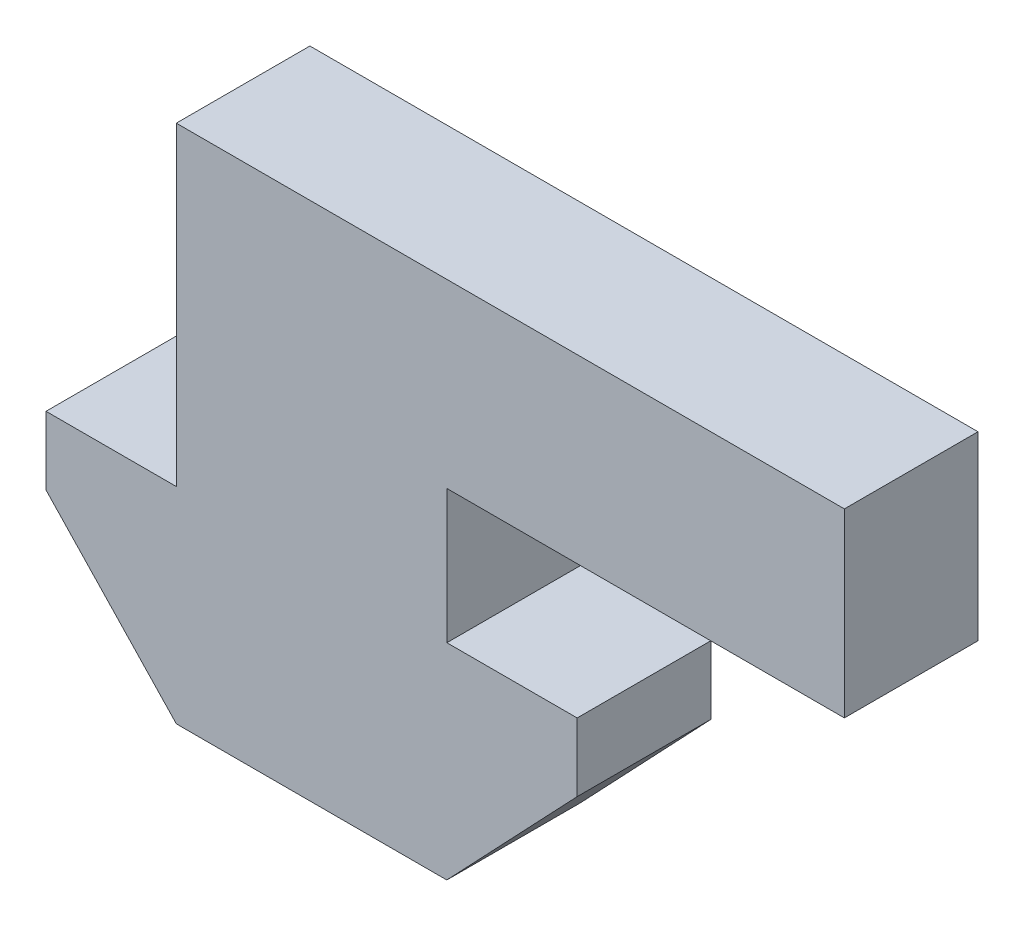
SolidWorks part; units mm, degrees
ref_plane "Front Plane" through (0, 0, 0) normal (0, 0, 1) x (1, 0, 0)
ref_plane "Top Plane" through (0, 0, 0) normal (0, 1, 0) x (1, 0, 0)
ref_plane "Right Plane" through (0, 0, 0) normal (1, 0, 0) x (0, 0, -1)
sketch "Sketch1" plane through (0, 0, 0) normal (0, 0, 1) x (1, 0, 0)
  line L0 (-4.05, 0) -> (-4.05, 9.42)
  line L1 (-4.05, 9.42) -> (15.95, 9.42)
  line L2 (15.95, 9.42) -> (15.95, 4)
  line L3 (15.95, 4) -> (4.05, 4)
  line L4 (4.05, 4) -> (4.05, 0)
  line B0 (7.95, 0) -> (7.95, -2.04)
  line B1 (4.048, -6.1524) -> (-4.048, -6.1524)
  line B2 (-7.95, -2.04) -> (-7.95, 0)
  line B3 (-7.95, 0) -> (7.95, 0)
  line B4 (7.95, -2.04) -> (4.048, -6.1524)
  line B5 (-4.048, -6.1524) -> (-7.95, -2.04)
  line B6 (4.05, 0) -> (-4.05, 0) construction
sketch_block_instance "Extrusion Profile-2"
sketch_block "Extrusion Profile" parameters "D1"=8.44, "D2"=2.6, "D3"=6, "D4"=16.7, "D6"=5.6686, "D7"=2.0404, "D8"=8.0963, "D9"=15.9, "D5"=2.4157
extrude "Boss-Extrude1" add sketch "Sketch1" along normal blind 4 contours B2 B5 B1 B4 B0 B3 | L0 B3 L4 L3 L2 L1
